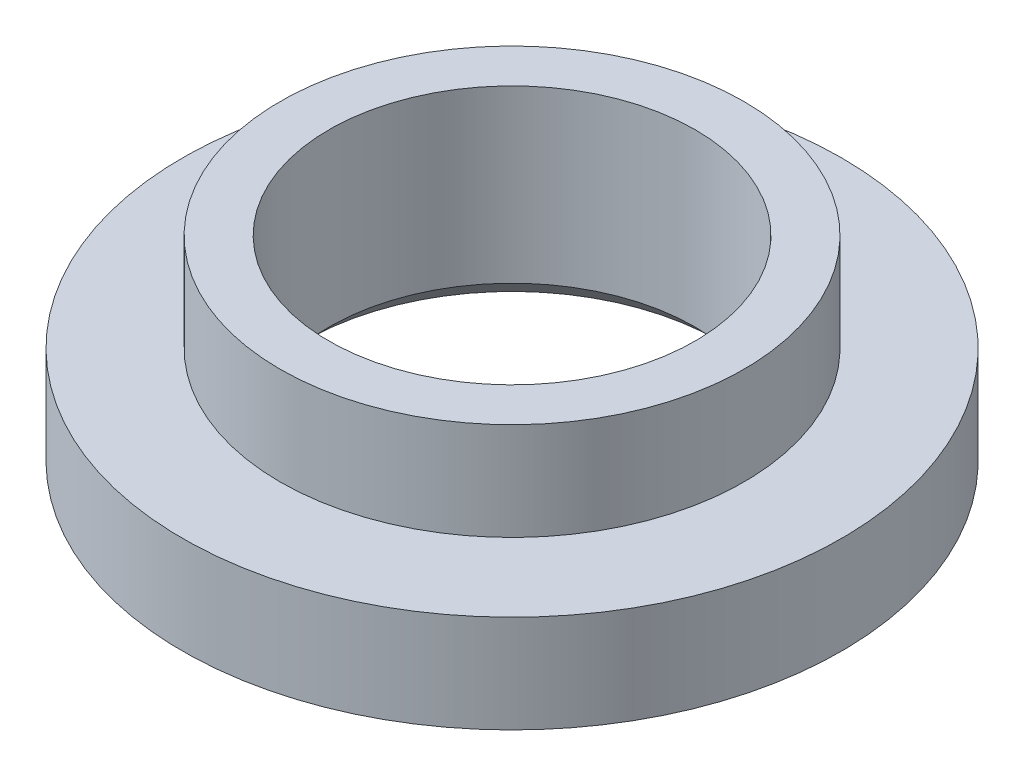
SolidWorks part; units mm, degrees
ref_plane "Front Plane" through (0, 0, 0) normal (0, 0, 1) x (1, 0, 0)
ref_plane "Top Plane" through (0, 0, 0) normal (0, 1, 0) x (1, 0, 0)
ref_plane "Right Plane" through (0, 0, 0) normal (1, 0, 0) x (0, 0, -1)
sketch "Sketch1" plane through (0, 0, 0) normal (0, 0, 1) x (1, 0, 0)
  line L0 (1.5, 0) -> (2.7, 0)
  line L1 (2.7, 0) -> (2.7, 0.8)
  line L2 (2.7, 0.8) -> (1.9, 0.8)
  line L3 (1.9, 0.8) -> (1.9, 1.6)
  line L4 (1.9, 1.6) -> (1.5, 1.6)
  line L5 (1.5, 1.6) -> (1.5, 0)
  line L6 (0, 0) -> (0, 1.6) construction
  point P9 (0, 0)
  dimension "D1" = 0.8
  dimension "D2" = 0.8
  dimension "D3" = 3
  dimension "D4" = 3.8
  dimension "D5" = 0.8
revolve "Revolve1" add sketch "Sketch1" angle 360 about L6
chamfer "Chamfer1" distance 0.2 angle 45 1 edges at (0, 0, -1.5)
